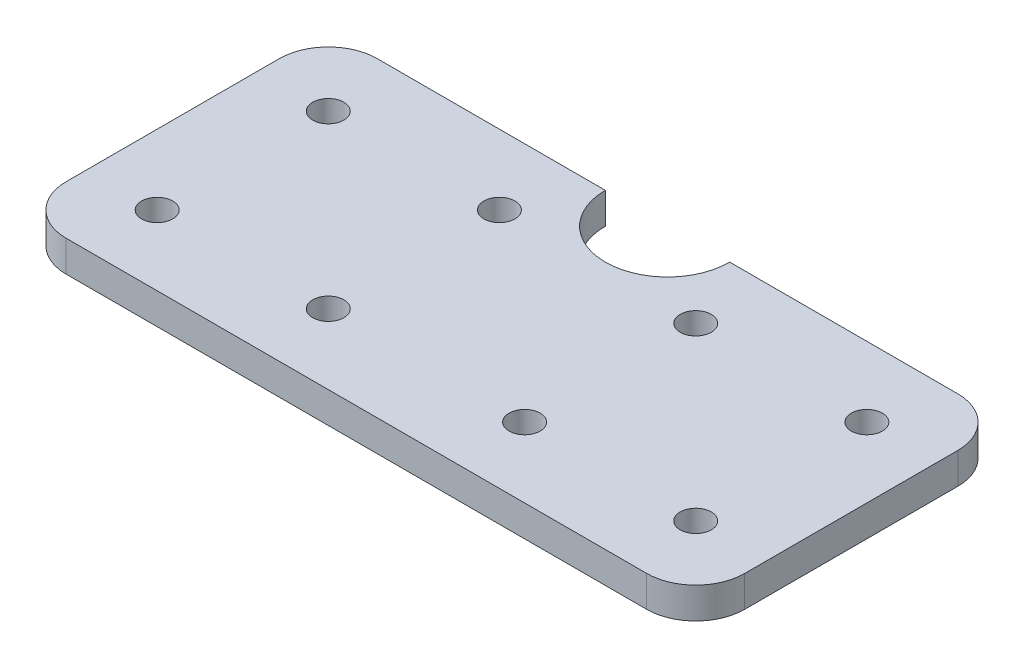
SolidWorks part; units mm, degrees
ref_plane "Front Plane" through (0, 0, 0) normal (0, 0, 1) x (1, 0, 0)
ref_plane "Top Plane" through (0, 0, 0) normal (0, 1, 0) x (1, 0, 0)
ref_plane "Right Plane" through (0, 0, 0) normal (1, 0, 0) x (0, 0, -1)
sketch "Sketch1" plane through (0, 0, 0) normal (0, 1, 0) x (1, 0, 0)
  line L1 (-69.25, -31.75) -> (69.25, -31.75)
  line L2 (-69.25, -31.75) -> (-69.25, 31.75)
  line L3 (-69.25, 31.75) -> (69.25, 31.75)
  line L4 (69.25, -31.75) -> (69.25, 31.75)
  line L5 (-69.25, -31.75) -> (69.25, 31.75) construction
  line L6 (-69.25, 31.75) -> (69.25, -31.75) construction
  point P0 (0, 0)
  dimension "D1" = 63.5
  dimension "D2" = 138.5
extrude "Boss-Extrude1" add sketch "Sketch1" along normal blind 6.35
sketch "Sketch2" plane through (0, 6.35, 0) normal (0, 1, 0) x (1, 0, 0)
  line L0 (0, 4.571) -> (0, 14.646) construction
  line L1 (0, 0) -> (10.2652, 0) construction
  circle A0 centre (-54.9625, 17.4625) radius 3.175
  circle A4 centre (-20.0375, 17.4625) radius 3.175
  circle A5 centre (20.0375, 17.4625) radius 3.175
  circle A6 centre (54.9625, 17.4625) radius 3.175
  circle A7 centre (54.9625, -17.4625) radius 3.175
  circle A8 centre (20.0375, -17.4625) radius 3.175
  circle A9 centre (-20.0375, -17.4625) radius 3.175
  circle A10 centre (-54.9625, -17.4625) radius 3.175
  dimension "D1" = 6.35
  dimension "D2" = 54.9625
  dimension "D3" = 17.4625
  dimension "D4" = 6.35
  dimension "D5" = 34.925
extrude "Cut-Extrude1" cut sketch "Sketch2" against normal blind 6.35
fillet "Fillet1" radius 10 4 edges at (-69.25, 3.175, 31.75) (69.25, 3.175, 31.75) (69.25, 3.175, -31.75) (-69.25, 3.175, -31.75)
sketch "Sketch3" plane through (0, 6.35, 0) normal (0, 1, 0) x (1, 0, 0)
  line L4 (0, 0) -> (-64.7181, 0) construction
  line L5 (-12.7, 31.75) -> (12.7, 31.75)
  arc A1 (12.7, 31.75) -> (-12.7, 31.75) centre (0, 31.75) cw
extrude "Cut-Extrude4" cut sketch "Sketch3" against normal blind 6.35
